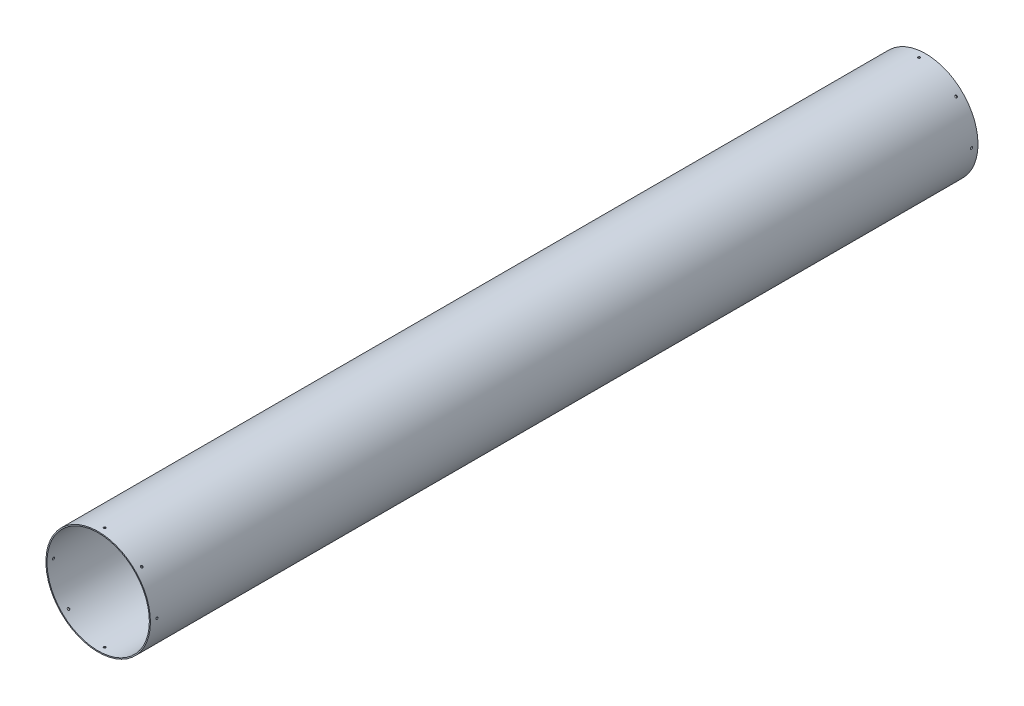
SolidWorks part; units mm, degrees
material "6061-T6 (SS)"
ref_plane "Front Plane" through (0, 0, 0) normal (0, 0, 1) x (1, 0, 0)
ref_plane "Top Plane" through (0, 0, 0) normal (0, 1, 0) x (1, 0, 0)
ref_plane "Right Plane" through (0, 0, 0) normal (1, 0, 0) x (0, 0, -1)
sketch "Sketch1" plane through (0, 0, 0) normal (0, 0, 1) x (1, 0, 0)
  circle A0 centre (0, 0) radius 152.4
  dimension "D1" = 304.8
extrude "Boss-Extrude1" add sketch "Sketch1" along normal blind 2413 contours A0
sketch "Sketch2" plane through (0, 0, 2413) normal (0, 0, 1) x (1, 0, 0)
  circle A0 centre (0, 0) radius 149.225
  dimension "D1" = 298.45
extrude "Cut-Extrude1" cut sketch "Sketch2" against normal blind 2413 contours A0
sketch "Sketch3" plane through (0, 0, 0) normal (0, 1, 0) x (1, 0, 0)
  line L0 (0, 0) -> (0, -19.05) construction
  circle A0 centre (0, -19.05) radius 3.175
  dimension "D1" = 6.35
  dimension "D2" = 19.05
extrude "Cut-Extrude2" cut sketch "Sketch3" along normal blind 190.5 contours A0
pattern_circular "CirPattern3" count 8 over 360 about axis through (0, 0, 0) along (0, 0, 1) of "Cut-Extrude2"
sketch "Sketch4" plane through (0, 0, 0) normal (0, 1, 0) x (1, 0, 0)
  line L0 (0, -2393.95) -> (0, 0)
  line L1 (-152.4, -2413) -> (152.4, -2413) construction
  line L2 (0, -2413) -> (0, -2393.95) construction
  circle A0 centre (0, -2393.95) radius 3.175
  dimension "D1" = 6.35
  dimension "D2" = 2393.95
extrude "Cut-Extrude4" cut sketch "Sketch4" against normal blind 270.764 contours A0
pattern_circular "CirPattern5" count 8 over 360 about axis through (0, 0, 2413) along (0, 0, 1) of "Cut-Extrude4"
equation "\"Rocket Diameter\"= 12in"
equation "\"D1@Sketch1\"=\"Rocket Diameter\""
equation "\"Airframe Thickness\"= 0.125in"
equation "\"Length\" = 95"
equation "\"D1@Boss-Extrude1\"=\"Length\""
equation "\"D1@Cut-Extrude1\"=\"Length\""
equation "\"Bolt Diameter\"= 0.25in"
equation "\"D1@Sketch3\"=\"Bolt Diameter\""
equation "\"D1@Sketch2\"= \"Rocket Diameter\"-\"Airframe Thickness\"*2"
equation "\"D1@Sketch4\"=\"Bolt Diameter\""
equation "\"D2@Sketch4\"=\"Length\"-\"Bolt_Distance\""
equation "\"Bolt_Distance\"= 0.75'distance from edge of airframe to bolt hole"
equation "\"D2@Sketch3\"=\"Bolt_Distance\""
